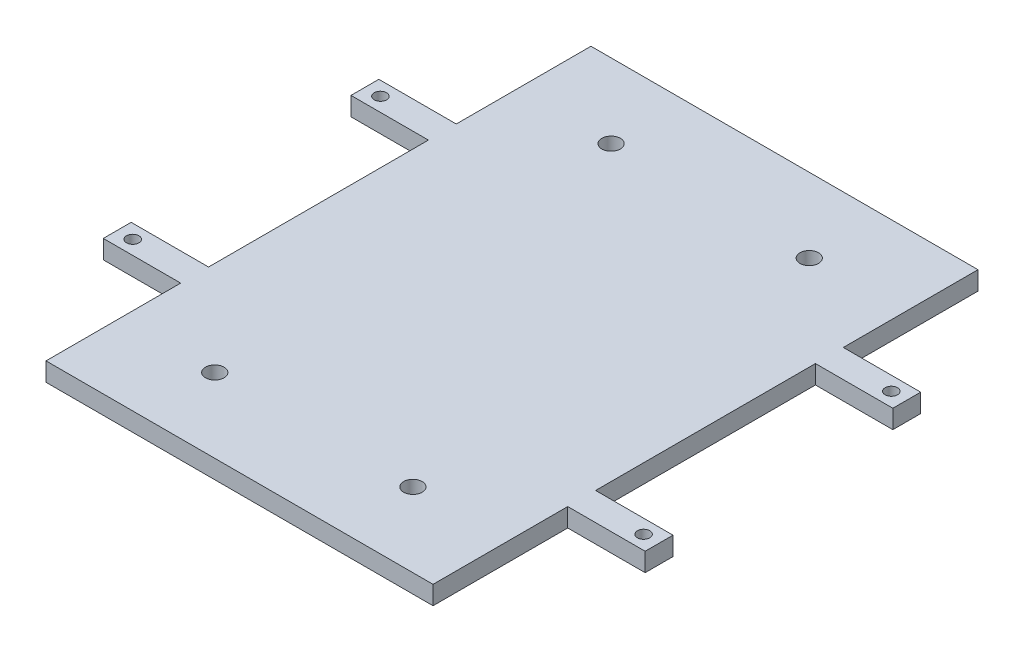
SolidWorks part; units mm, degrees
ref_plane "Front Plane" through (0, 0, 0) normal (0, 0, 1) x (1, 0, 0)
ref_plane "Top Plane" through (0, 0, 0) normal (0, 1, 0) x (1, 0, 0)
ref_plane "Right Plane" through (0, 0, 0) normal (1, 0, 0) x (0, 0, -1)
sketch "Sketch1" plane through (0, 0, 0) normal (0, 1, 0) x (1, 0, 0)
  line L0 (0, 0) -> (-31.25, 0) construction
  line L1 (-31.25, -44) -> (31.25, -44) construction
  line L2 (-31.25, -44) -> (-31.25, 17.75) construction
  line L3 (-31.25, 44) -> (31.25, 44) construction
  line L4 (31.25, -44) -> (31.25, 44) construction
  line L5 (-31.25, -44) -> (31.25, 44) construction
  line L6 (-31.25, 44) -> (31.25, -44) construction
  line L7 (-43.75, 22.25) -> (-31.25, 22.25)
  line L8 (-43.75, 22.25) -> (-43.75, 17.75)
  line L9 (-43.75, 17.75) -> (-31.25, 17.75)
  line L11 (-43.75, 22.25) -> (-31.25, 17.75) construction
  line L12 (-43.75, 17.75) -> (-31.25, 22.25) construction
  line L13 (-31.25, 22.25) -> (-31.25, 44) construction
  line L14 (-43.75, -17.75) -> (-31.25, -17.75)
  line L15 (-43.75, -22.25) -> (-43.75, -17.75)
  line L16 (-43.75, -22.25) -> (-31.25, -22.25)
  line L17 (0, 0) -> (0, 44) construction
  line L18 (-31.25, -17.75) -> (-31.25, 17.75)
  line L19 (31.25, 44) -> (-31.25, 44)
  line L20 (-31.25, 44) -> (-31.25, 22.25)
  line L21 (-31.25, -44) -> (-31.25, -22.25)
  line L22 (31.25, -44) -> (-31.25, -44)
  line L23 (31.25, -44) -> (31.25, -22.25)
  line L24 (43.75, -22.25) -> (31.25, -22.25)
  line L25 (43.75, -22.25) -> (43.75, -17.75)
  line L26 (43.75, -17.75) -> (31.25, -17.75)
  line L27 (31.25, -17.75) -> (31.25, 17.75)
  line L28 (43.75, 17.75) -> (31.25, 17.75)
  line L29 (43.75, 22.25) -> (43.75, 17.75)
  line L30 (43.75, 22.25) -> (31.25, 22.25)
  line L31 (31.25, 44) -> (31.25, 22.25)
  point P0 (0, 0)
  point P6 (-37.5, 20)
  point P19 (0, -44)
  dimension "D1" = 62.5
  dimension "D2" = 88
  dimension "D3" = 12.5
  dimension "D4" = 4.5
  dimension "D5" = 20
extrude "Boss-Extrude1" add sketch "Sketch1" along normal blind 3
sketch "Sketch2" plane through (0, 0, 0) normal (0, -1, 0) x (1, 0, 0)
  line L0 (-43.75, 17.75) -> (-43.75, 22.25) construction
  line L1 (-31.25, 22.25) -> (-31.25, 44) construction
  line L2 (0, 0) -> (-31.25, 0) construction
  line L3 (-31.25, -17.75) -> (-31.25, 17.75) construction
  line L4 (0, 0) -> (0, 44) construction
  line L5 (-31.25, 44) -> (31.25, 44) construction
  circle A0 centre (-41.25, 20) radius 1
  circle A1 centre (-41.25, -20) radius 1
  circle A2 centre (41.25, -20) radius 1
  circle A3 centre (41.25, 20) radius 1
  point P5 (-43.75, 20)
  point P12 (0, 0)
  dimension "D2" = 2
  dimension "D1" = 10
extrude "Cut-Extrude1" cut sketch "Sketch2" against normal blind 6
sketch "Sketch3" plane through (0, 3, 0) normal (0, 1, 0) x (1, 0, 0)
  line L1 (16, -32) -> (-16, -32) construction
  line L2 (16, -32) -> (16, 32) construction
  line L3 (16, 32) -> (-16, 32) construction
  line L4 (-16, -32) -> (-16, 32) construction
  line L5 (16, -32) -> (-16, 32) construction
  line L6 (16, 32) -> (-16, -32) construction
  circle A0 centre (-16, 32) radius 1.5
  circle A1 centre (16, 32) radius 1.5
  circle A2 centre (16, -32) radius 1.5
  circle A3 centre (-16, -32) radius 1.5
  point P0 (0, 0)
  dimension "D3" = 3
  dimension "D1" = 32
  dimension "D2" = 64
extrude "Cut-Extrude2" cut sketch "Sketch3" against normal blind 10
